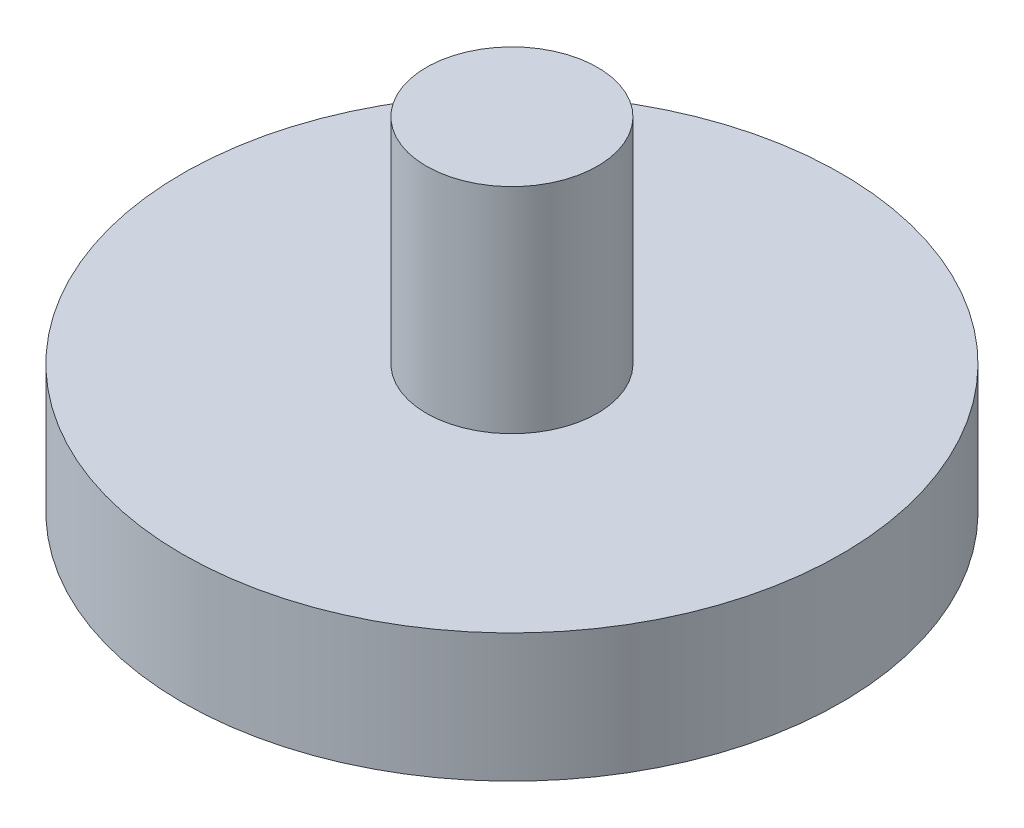
SolidWorks part; units mm, degrees
ref_plane "Ön Düzlem" through (0, 0, 0) normal (0, 0, 1) x (1, 0, 0)
ref_plane "Üst Düzlem" through (0, 0, 0) normal (0, 1, 0) x (1, 0, 0)
ref_plane "Sağ Düzlem" through (0, 0, 0) normal (1, 0, 0) x (0, 0, -1)
sketch "Sketch1" plane through (0, 0, 0) normal (0, 1, 0) x (1, 0, 0)
  circle A0 centre (0, 0) radius 7.7
  dimension "D1" = 15.4
extrude "Boss-Extrude1" add sketch "Sketch1" along normal blind 3
sketch "Sketch2" plane through (0, 3, 0) normal (0, 1, 0) x (1, 0, 0)
  circle A0 centre (0, 0) radius 2
  dimension "D1" = 4
extrude "Boss-Extrude2" add sketch "Sketch2" along normal blind 5
sketch "Sketch3" plane through (0, 0, 0) normal (0, -1, 0) x (1, 0, 0)
  circle A0 centre (0, 0) radius 1.5
  dimension "D1" = 3
extrude "Cut-Extrude1" cut sketch "Sketch3" against normal blind 5
